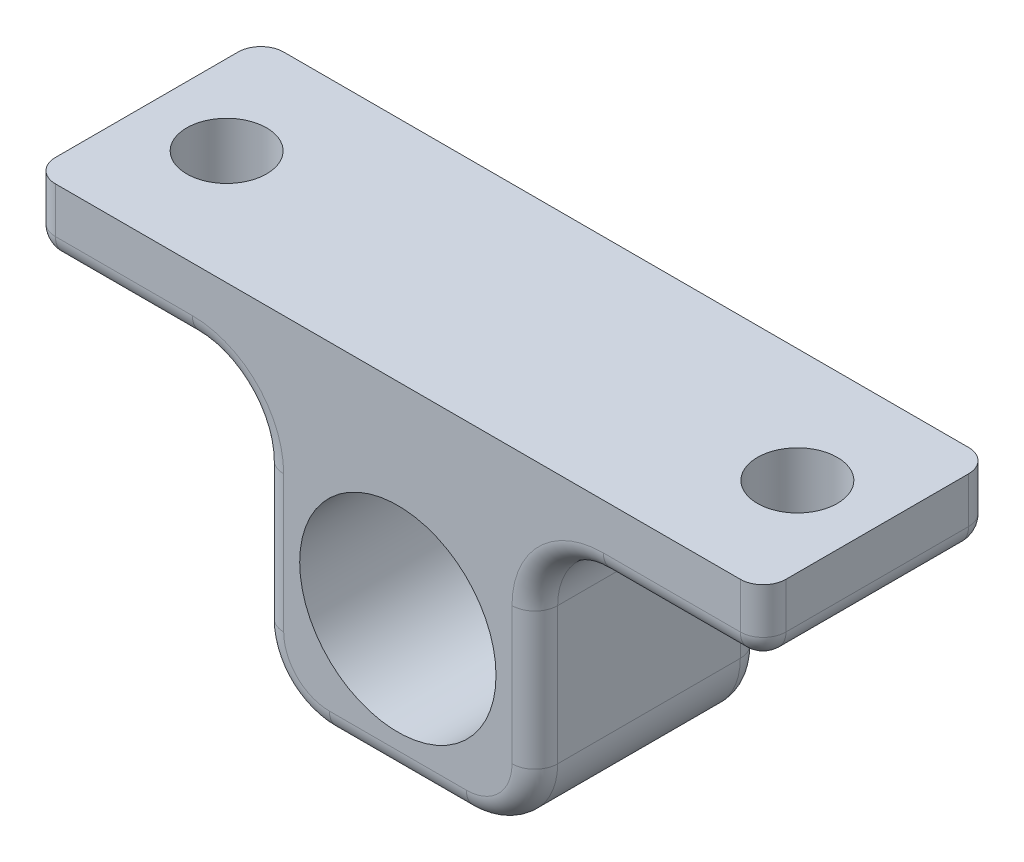
SolidWorks part; units mm, degrees
ref_plane "正面" through (0, 0, 0) normal (0, 0, 1) x (1, 0, 0)
ref_plane "平面" through (0, 0, 0) normal (0, 1, 0) x (1, 0, 0)
ref_plane "右側面" through (0, 0, 0) normal (1, 0, 0) x (0, 0, -1)
sketch "ｽｹｯﾁ1" plane through (0, 0, 0) normal (0, 0, 1) x (1, 0, 0)
  line L0 (1, 10) -> (1, -5)
  line L1 (7, -5) -> (-5, -5)
  line L2 (7, -5) -> (7, 10)
  line L3 (7, 10) -> (-5, 10)
  line L4 (-5, -5) -> (-5, 10)
  line L5 (7, 10) -> (17, 10)
  line L6 (7, 10) -> (7, 7)
  line L7 (7, 7) -> (17, 7)
  line L8 (17, 10) -> (17, 7)
  line L9 (-15, 10) -> (-15, 7)
  line L10 (-5, 7) -> (-15, 7)
  line L11 (-5, 10) -> (-5, 7)
  line L12 (-5, 10) -> (-15, 10)
  line L13 (7, -5) -> (7, 10)
  line L14 (-5, -5) -> (-5, 10)
  line L15 (7, 10) -> (17, 10)
  line L16 (17, 10) -> (7, 10)
  dimension "D1" = 15
  dimension "D2" = 12
  dimension "D5" = 3
  dimension "D6" = 10
extrude "ﾎﾞｽ - 押し出し1" add sketch "ｽｹｯﾁ1" along normal blind 10 contours L2 L3 L0 L1 | L8 L5 L2 L7 | L4 L1 L0 L3 | L4 L12 L9 L10
sketch "ｽｹｯﾁ2" plane through (0, 0, 0) normal (0, 0, -1) x (-1, 0, 0)
  line L0 (-1, -5) -> (-1, 10) construction
  line L3 (-7, -5) -> (5, -5) construction
  line L4 (-17, 10) -> (15, 10) construction
  circle A0 centre (-1, 1) radius 4.3
  dimension "D1" = 8.6
  dimension "D2" = 6
extrude "ｶｯﾄ - 押し出し1" cut sketch "ｽｹｯﾁ2" against normal through all
sketch "ｽｹｯﾁ3" plane through (0, 7, 0) normal (0, -1, 0) x (1, 0, 0)
  line L0 (-15, 10) -> (-15, 0) construction
  line L1 (-5, 0) -> (-15, 0) construction
  line L2 (0, 0.3201) -> (0, 10.158)
  line L3 (7, 0) -> (17, 0) construction
  line L4 (17, 10) -> (17, 0) construction
  circle A0 centre (-11.5, 5) radius 1.75
  circle A1 centre (13.5, 5) radius 1.75
  dimension "D1" = 3.5
  dimension "D4" = 3.5
  dimension "D5" = 5
  dimension "D6" = 3.5
  dimension "D2" = 3.5
  dimension "D3" = 5
extrude "ｶｯﾄ - 押し出し2" cut sketch "ｽｹｯﾁ3" against normal through all contours A0 | A1
fillet "ﾌｨﾚｯﾄ1" radius 3 4 edges at (-5, 7, 5) (7, 7, 5) (-5, -5, 5) (7, -5, 5)
fillet "ﾌｨﾚｯﾄ2" radius 1 24 edges at (13.5, 7, 10) (13.5, 7, 0) (7.8787, 6.1213, 10) (7.8787, 6.1213, 0) (7, 1, 0) (7, 1, 10) (6.1213, -4.1213, 10) (6.1213, -4.1213, 0) (1, -5, 10) (1, -5, 0) (-4.1213, -4.1213, 10) (-4.1213, -4.1213, 0) (-5, 1, 10) (-5, 1, 0) (-5.8787, 6.1213, 10) (-5.8787, 6.1213, 0) (-15, 8.5, 0) (-15, 8.5, 10) (17, 8.5, 0) (17, 8.5, 10) (17, 7, 5) (-11.5, 7, 0) (-11.5, 7, 10) (-15, 7, 5)
